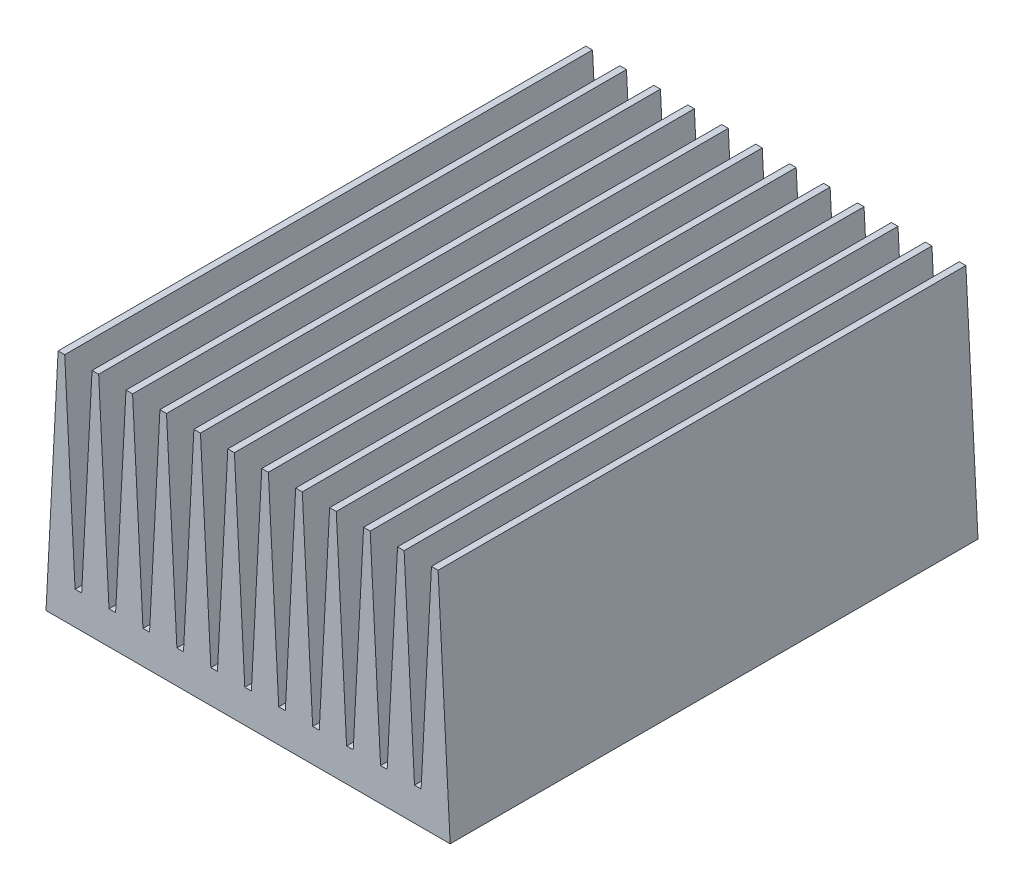
SolidWorks part; units mm, degrees
ref_plane "Front Plane" through (0, 0, 0) normal (0, 0, 1) x (1, 0, 0)
ref_plane "Top Plane" through (0, 0, 0) normal (0, 1, 0) x (1, 0, 0)
ref_plane "Right Plane" through (0, 0, 0) normal (1, 0, 0) x (0, 0, -1)
sketch "Sketch2" plane through (0, 0, 0) normal (0, 0, 1) x (1, 0, 0)
  line L1 (-20.6579, -2.5) -> (20.6579, -2.5)
  line L3 (-20.6579, 2.5) -> (-19.7599, 2.5)
  line L5 (-20.6579, -2.5) -> (0, 0) construction
  line L6 (-20.6579, 2.5) -> (20.6579, -2.5) construction
  line L7 (18.8236, 32.5) -> (17.8236, 32.5)
  line L8 (17.8236, 32.5) -> (16.2514, 2.5)
  line L9 (18.3236, 32.5) -> (18.3236, 2.5) construction
  line L10 (20.3959, 2.5) -> (20.6579, -2.5)
  line L12 (20.3959, 2.5) -> (18.8236, 32.5)
  line L13 (15.2514, 2.5) -> (13.6792, 32.5)
  line L14 (13.6792, 32.5) -> (12.6792, 32.5)
  line L15 (12.6792, 32.5) -> (11.1069, 2.5)
  line L17 (10.1069, 2.5) -> (8.5347, 32.5)
  line L18 (8.5347, 32.5) -> (7.5347, 32.5)
  line L19 (7.5347, 32.5) -> (5.9625, 2.5)
  line L21 (4.9625, 2.5) -> (3.3902, 32.5)
  line L22 (3.3902, 32.5) -> (2.3902, 32.5)
  line L23 (2.3902, 32.5) -> (0.818, 2.5)
  line L25 (-0.182, 2.5) -> (-1.7542, 32.5)
  line L26 (-1.7542, 32.5) -> (-2.7542, 32.5)
  line L27 (-2.7542, 32.5) -> (-4.3265, 2.5)
  line L29 (-5.3265, 2.5) -> (-6.8987, 32.5)
  line L30 (-6.8987, 32.5) -> (-7.8987, 32.5)
  line L31 (-7.8987, 32.5) -> (-9.4709, 2.5)
  line L33 (-10.4709, 2.5) -> (-12.0432, 32.5)
  line L34 (-12.0432, 32.5) -> (-13.0432, 32.5)
  line L35 (-13.0432, 32.5) -> (-14.6154, 2.5)
  line L37 (-15.6154, 2.5) -> (-17.1876, 32.5)
  line L38 (-17.1876, 32.5) -> (-18.1876, 32.5)
  line L39 (-18.1876, 32.5) -> (-19.7599, 2.5)
  line L41 (-20.7599, 2.5) -> (-22.3321, 32.5)
  line L42 (-22.3321, 32.5) -> (-23.3321, 32.5)
  line L43 (-23.3321, 32.5) -> (-24.9043, 2.5)
  line L45 (-25.9043, 2.5) -> (-27.4766, 32.5)
  line L46 (-27.4766, 32.5) -> (-28.4766, 32.5)
  line L47 (-28.4766, 32.5) -> (-30.0488, 2.5)
  line L49 (-31.0488, 2.5) -> (-32.621, 32.5)
  line L50 (-32.621, 32.5) -> (-33.621, 32.5)
  line L51 (-33.621, 32.5) -> (-35.1933, 2.5)
  line L53 (-36.1933, 2.5) -> (-37.7655, 32.5)
  line L54 (-37.7655, 32.5) -> (-38.7655, 32.5)
  line L55 (-38.7655, 32.5) -> (-40.3377, 2.5)
  line L56 (-40.3377, 2.5) -> (-40.5998, -2.5)
  line L57 (-40.5998, -2.5) -> (-20.6579, -2.5)
  line L58 (-36.1933, 2.5) -> (-35.1933, 2.5)
  line L59 (-31.0488, 2.5) -> (-30.0488, 2.5)
  line L63 (-25.9043, 2.5) -> (-24.9043, 2.5)
  line L65 (-20.7599, 2.5) -> (-19.7599, 2.5)
  line L66 (-15.6154, 2.5) -> (-14.6154, 2.5)
  line L68 (-15.6154, 2.5) -> (-14.6154, 2.5)
  line L70 (-10.4709, 2.5) -> (-9.4709, 2.5)
  line L71 (-10.4709, 2.5) -> (-9.4709, 2.5)
  line L73 (-5.3265, 2.5) -> (-4.3265, 2.5)
  line L74 (-5.3265, 2.5) -> (-4.3265, 2.5)
  line L76 (-0.182, 2.5) -> (0.818, 2.5)
  line L77 (-0.182, 2.5) -> (0.818, 2.5)
  line L79 (4.9625, 2.5) -> (5.9625, 2.5)
  line L80 (4.9625, 2.5) -> (5.9625, 2.5)
  line L82 (10.1069, 2.5) -> (11.1069, 2.5)
  line L83 (10.1069, 2.5) -> (11.1069, 2.5)
  line L85 (15.2514, 2.5) -> (16.2514, 2.5)
  line L86 (15.2514, 2.5) -> (16.2514, 2.5)
  point P0 (0, 0)
  dimension "D1" = 5
  dimension "D2" = 41.3158
  dimension "D3" = 87
  dimension "D4" = 1
  dimension "D5" = 35
  dimension "D7" = 1
  dimension "D6" = 12
extrude "Boss-Extrude1" add sketch "Sketch2" along normal blind 80 contours L85 L13 L14 L15 L82 L17 L18 L19 L79 L21 L22 L23 L76 L25 L26 L27 L73 L29 L30 L31 L70 L33 L34 L35 L66 L37 L38 L39 L3 L65 L41 L42 L43 L63 L45 L46 L47 L59 L49 L50 L51 L58 L53 L54 L55 L56 L57 L1 L10 L12 L7
